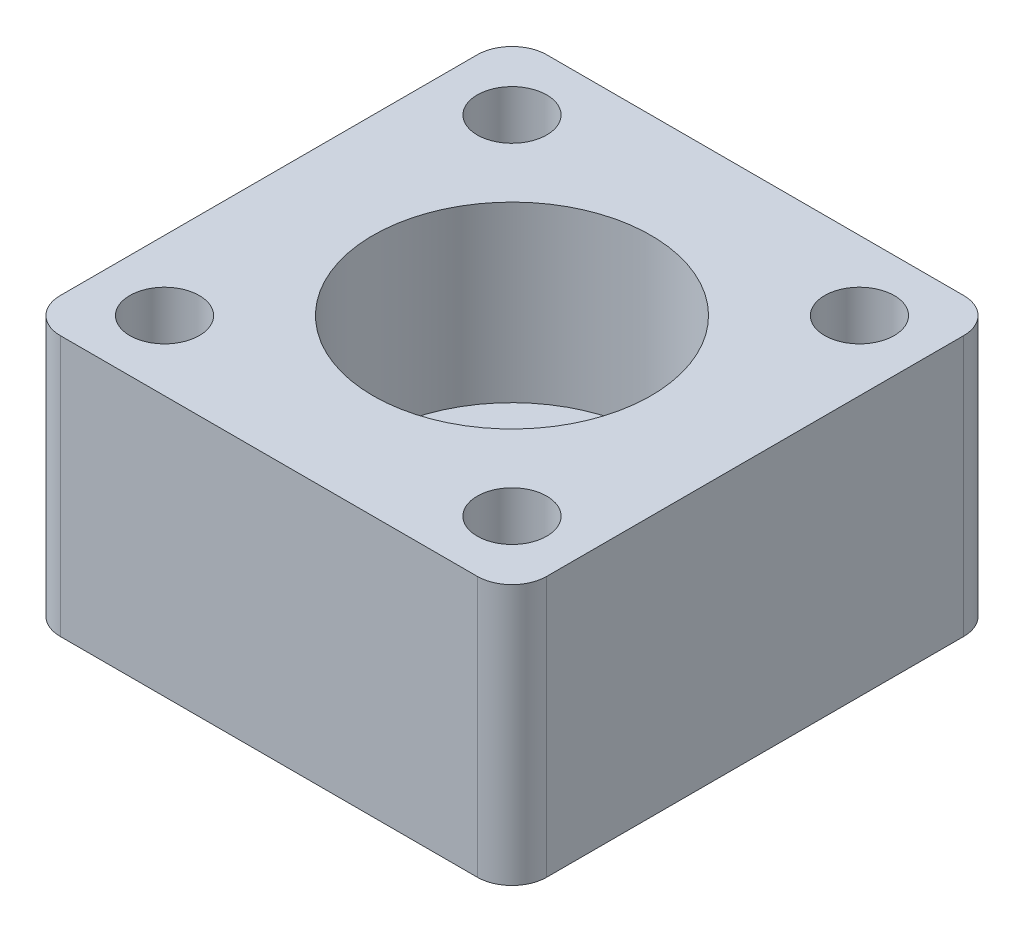
SolidWorks part; units mm, degrees
material "ABS PC"
ref_plane "Front Plane" through (0, 0, 0) normal (0, 0, 1) x (1, 0, 0)
ref_plane "Top Plane" through (0, 0, 0) normal (0, 1, 0) x (1, 0, 0)
ref_plane "Right Plane" through (0, 0, 0) normal (1, 0, 0) x (0, 0, -1)
sketch "Sketch1" plane through (0, 0, 0) normal (0, 1, 0) x (1, 0, 0)
  line L0 (0, 0) -> (0, 28)
  line L1 (0, 0) -> (28, 0)
  line L2 (0, 28) -> (28, 28)
  line L3 (28, 0) -> (28, 28)
  dimension "D1" = 28
  dimension "D2" = 28
extrude "Boss-Extrude1" add sketch "Sketch1" along normal blind 15
sketch "Sketch2" plane through (0, 15, 0) normal (0, 1, 0) x (-1, 0, 0)
  line L0 (-28, -28) -> (0, -28) construction
  line L1 (0, -28) -> (0, 0) construction
  circle A0 centre (-14, -14) radius 5
  circle A1 centre (-4, -24) radius 2
  circle A2 centre (-24, -24) radius 2
  circle A3 centre (-4, -4) radius 2
  circle A4 centre (-24, -4) radius 2
  dimension "D2" = 14
  dimension "D3" = 10
  dimension "D4" = 4
  dimension "D5" = 10
  dimension "D6" = 10
  dimension "D7" = 10
  dimension "D8" = 10
  dimension "D1" = 14
extrude "Cut-Extrude1" cut sketch "Sketch2" against normal through all
sketch "Sketch3" plane through (0, 15, 0) normal (0, 1, 0) x (1, 0, 0)
  circle A0 centre (14, 14) radius 8
  dimension "D1" = 16
extrude "Cut-Extrude2" cut sketch "Sketch3" against normal blind 10
fillet "Fillet1" radius 2 4 edges at (0, 7.5, 0) (28, 7.5, 0) (28, 7.5, -28) (0, 7.5, -28)
